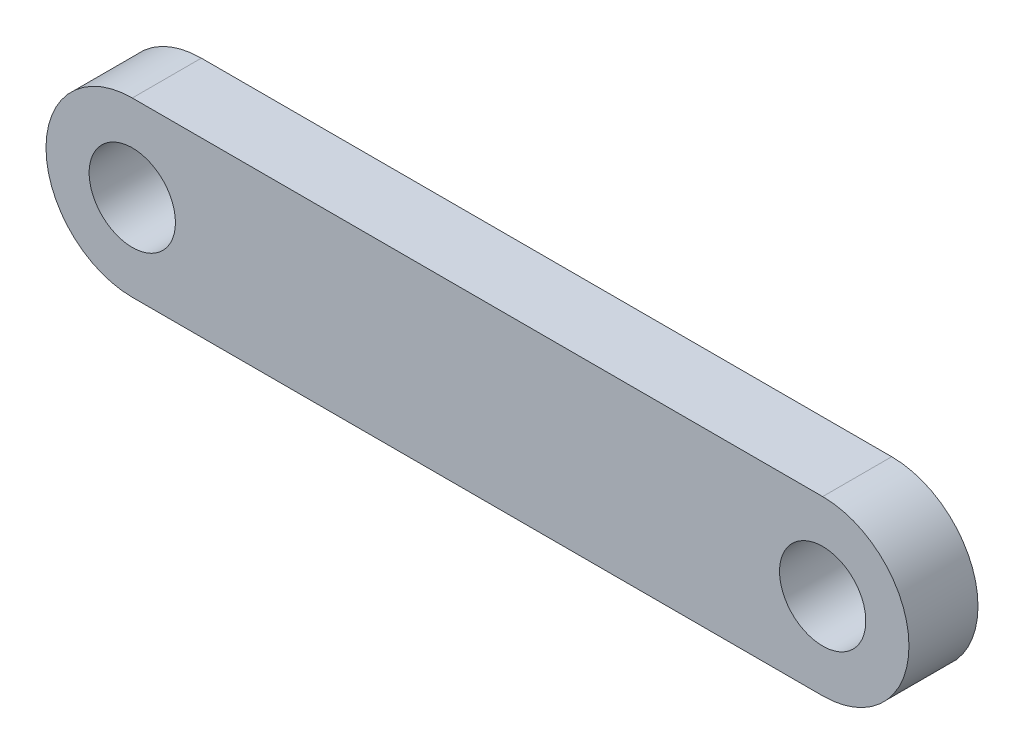
SolidWorks part; units mm, degrees
ref_plane "Front Plane" through (0, 0, 0) normal (0, 0, 1) x (1, 0, 0)
ref_plane "Top Plane" through (0, 0, 0) normal (0, 1, 0) x (1, 0, 0)
ref_plane "Right Plane" through (0, 0, 0) normal (1, 0, 0) x (0, 0, -1)
sketch "Sketch1" plane through (0, 0, 0) normal (0, 0, 1) x (1, 0, 0)
  line L0 (-25.4, 0) -> (25.4, 0) construction
  line L1 (-25.4, 6.35) -> (25.4, 6.35)
  line L2 (-25.4, -6.35) -> (25.4, -6.35)
  line L3 (0, -13.97) -> (0, 13.97) construction
  arc A0 (-25.4, 6.35) -> (-25.4, -6.35) centre (-25.4, 0) ccw
  arc A1 (25.4, -6.35) -> (25.4, 6.35) centre (25.4, 0) ccw
  circle A2 centre (-25.4, 0) radius 3.175
  circle A3 centre (25.4, 0) radius 3.175
  point P3 (0, 0)
  dimension "D1" = 6.35
  dimension "D3" = 6.35
  dimension "D2" = 50.8
extrude "Boss-Extrude1" add sketch "Sketch1" along normal blind 5.08
